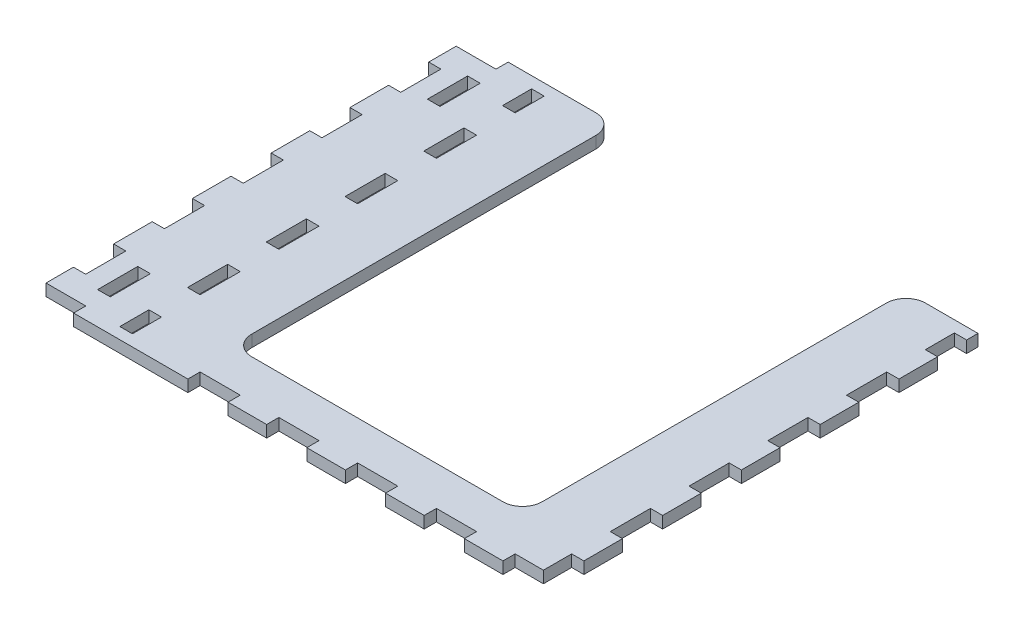
SolidWorks part; units mm, degrees
ref_plane "Front Plane" through (0, 0, 0) normal (0, 0, 1) x (1, 0, 0)
ref_plane "Top Plane" through (0, 0, 0) normal (0, 1, 0) x (1, 0, 0)
ref_plane "Right Plane" through (0, 0, 0) normal (1, 0, 0) x (0, 0, -1)
sketch "Sketch1" plane through (0, 0, 0) normal (0, 1, 0) x (1, 0, 0)
  line L0 (0, 0) -> (0, 21) construction
  line L1 (-114.8722, 48.0292) -> (-111.8722, 48.0292) construction
  line L2 (-66.1222, -11.6708) -> (-66.4222, -11.6708) construction
  line L3 (-66.4222, 40.2014) -> (-66.4222, -63.543) construction
  line L4 (-70.9222, -63.543) -> (-70.9222, 40.2014) construction
  line L5 (21.0585, -66.843) -> (-21.0585, -66.843) construction
  line L6 (-55.1722, 43.5014) -> (55.1722, 43.5014) construction
  line L7 (-55.1722, 43.5014) -> (-55.1722, -66.843) construction
  line L8 (-55.1722, -66.843) -> (55.1722, -66.843) construction
  line L9 (-66.4222, 43.5014) -> (-66.4222, -66.843) construction
  line L10 (-70.9222, -66.843) -> (-70.9222, 43.5014) construction
  line L11 (-70.9222, -11.6708) -> (-71.2222, -11.6708) construction
  line L12 (-55.1722, -63.843) -> (-74.2222, -63.843) construction
  line L13 (55.1722, 43.5014) -> (55.1722, -66.843)
  line L14 (-114.8722, -7.143) -> (-4.5278, -7.143) construction
  line L15 (36.8722, 43.5014) -> (36.8722, -66.843)
  line L16 (-36.8722, -66.843) -> (-36.8722, 43.5014)
  line L17 (36.8722, 99.9014) -> (36.8722, -3.843) construction
  line L18 (-55.1722, 43.5014) -> (-74.2222, 43.5014) construction
  line L19 (-74.2222, 43.5014) -> (-74.2222, -66.843)
  line L20 (-74.2222, -66.843) -> (-55.1722, -66.843) construction
  line L21 (-67.1722, 43.5014) -> (-67.1722, -66.843) construction
  line L22 (-70.1722, -66.843) -> (-70.1722, 43.5014) construction
  line L23 (-70.1722, -11.6708) -> (-67.1722, -11.6708) construction
  line L24 (-74.2222, -66.843) -> (-36.8722, -66.843)
  line L25 (-36.8722, -66.843) -> (-36.7807, -66.8623)
  line L26 (36.8722, -66.843) -> (55.1722, -66.843)
  line L27 (55.1722, 43.5014) -> (36.8722, 43.5014)
  line L28 (-71.2222, -66.843) -> (-71.2222, 43.5014) construction
  line L29 (-66.1222, -66.843) -> (-66.1222, 43.5014) construction
  line L30 (-74.2222, 40.5014) -> (-55.1722, 40.5014) construction
  line L31 (-63.1222, -66.843) -> (-63.1222, 43.5014) construction
  line L32 (-55.1722, -63.843) -> (55.1722, -63.843) construction
  line L33 (-36.8722, 43.5014) -> (-74.2222, 43.5014)
  line L34 (21.0585, -63.843) -> (-21.0585, -63.843) construction
  line L35 (0, -63.843) -> (0, -66.843) construction
  line L36 (-71.2222, -11.6708) -> (-74.2222, -11.6708) construction
  line L37 (-66.1222, -11.6708) -> (-63.1222, -11.6708) construction
  line L38 (-52.1722, -66.843) -> (-52.1722, 43.5014) construction
  line L39 (52.1722, -66.843) -> (52.1722, 43.5014) construction
  line L40 (52.1722, -11.6708) -> (55.1722, -11.6708) construction
  line L41 (-67.1722, -11.9708) -> (-55.1722, -11.9708) construction
  line L43 (-67.1722, -11.6708) -> (-55.1722, -11.6708) construction
  line L44 (-67.1722, -11.6708) -> (-66.8722, -11.6708) construction
  line L45 (-66.8722, -11.6708) -> (-66.8722, -11.9708) construction
  line L46 (0, -63.843) -> (0, -47.0292) construction
  line L47 (-35.0585, 12.9708) -> (-51.8722, 12.9708) construction
  line L48 (-35.0585, 12.9708) -> (-35.0585, 83.0877) construction
  line L49 (-35.0585, -47.0292) -> (35.0585, -47.0292) construction
  line L50 (-35.0585, -47.0292) -> (-35.0585, 23.0877) construction
  line L51 (-35.0585, 23.0877) -> (35.0585, 23.0877) construction
  line L52 (35.0585, -47.0292) -> (35.0585, 23.0877) construction
  line L53 (-36.8722, -48.843) -> (36.8722, -48.843) construction
  line L54 (35.0585, -47.0292) -> (35.0585, -48.843) construction
  line L55 (35.0585, -47.0292) -> (36.8722, -47.0292) construction
  circle A0 centre (0, 0) radius 21 construction
  circle A6 centre (0, 0) radius 21 construction
  dimension "D1" = 12
  dimension "D3" = 0.3
ref_plane "zplane" through (-67.1722, 0, 0) normal (1, 0, 0) x (0, 0, -1)
sketch "Sketch2" plane through (0, 0, 0) normal (0, 1, 0) x (1, 0, 0)
  line L0 (-74.2222, -66.843) -> (55.1722, -66.843)
  line L1 (-74.2222, -66.843) -> (-36.8722, -66.843) construction
  line L2 (-74.2222, -66.843) -> (-74.2222, 43.5014)
  line L3 (-74.2222, 43.5014) -> (-41.8722, 43.5014)
  line L4 (-36.8722, -66.843) -> (-36.8722, 43.5014) construction
  line L5 (41.8722, 43.5014) -> (55.1722, 43.5014)
  line L6 (36.8722, 43.5014) -> (36.8722, -66.843) construction
  line L7 (36.8722, -66.843) -> (55.1722, -66.843) construction
  line L8 (55.1722, 43.5014) -> (55.1722, -66.843)
  line L9 (-31.8722, -53.843) -> (31.8722, -53.843)
  line L10 (36.8722, -48.843) -> (36.8722, 38.5014)
  line L11 (-36.8722, -48.843) -> (-36.8722, 38.5014)
  line L12 (-36.8722, -48.843) -> (36.8722, -48.843) construction
  arc A0 (31.8722, -53.843) -> (36.8722, -48.843) centre (31.8722, -48.843) ccw
  arc A1 (-36.8722, -48.843) -> (-31.8722, -53.843) centre (-31.8722, -48.843) ccw
  arc A2 (41.8722, 43.5014) -> (36.8722, 38.5014) centre (41.8722, 38.5014) ccw
  arc A3 (-41.8722, 43.5014) -> (-36.8722, 38.5014) centre (-41.8722, 38.5014) cw
  point P16 (36.8722, -53.843)
  point P19 (-36.8722, -53.843)
  dimension "D1" = 5
  dimension "D3" = 5
  dimension "D2" = 13
extrude "Boss-Extrude1" add sketch "Sketch2" against normal up to vertex (3 mm away)
sketch "Sketch4" plane through (0, 0, 0) normal (0, 1, 0) x (1, 0, 0)
  line L0 (-74.2222, 43.5014) -> (-74.2222, -66.843) construction
  line L1 (-63.1222, -66.843) -> (-63.1222, 43.5014) construction
  line L2 (-71.2222, -66.843) -> (-71.2222, 43.5014) construction
  line L3 (-66.1222, -66.843) -> (-66.1222, 43.5014) construction
  line L4 (-74.2222, 43.5014) -> (-74.2222, -66.843) construction
  line L5 (-63.1222, -66.843) -> (-63.1222, 43.5014) construction
  line L6 (-71.2222, -66.843) -> (-71.2222, 43.5014) construction
  line L7 (-66.1222, -66.843) -> (-66.1222, 43.5014) construction
  line L8 (-74.2222, 40.5014) -> (-55.1722, 40.5014) construction
  line L9 (-36.8722, 43.5014) -> (-74.2222, 43.5014) construction
  line L10 (-74.2222, 40.5014) -> (-55.1722, 40.5014) construction
  line L11 (-36.8722, 43.5014) -> (-74.2222, 43.5014) construction
  line L12 (-74.2222, -66.843) -> (-36.8722, -66.843) construction
  line L13 (-55.1722, -63.843) -> (-74.2222, -63.843) construction
  line L14 (-74.2222, -66.843) -> (-36.8722, -66.843) construction
  line L15 (-55.1722, -63.843) -> (-74.2222, -63.843) construction
  line L16 (-55.1722, 33.3292) -> (-52.1722, 33.3292) construction
  line L17 (-55.1722, 23.3292) -> (-52.1722, 23.3292) construction
  line L18 (-55.1722, 13.3292) -> (-52.1722, 13.3292) construction
  line L19 (-55.1722, 3.3292) -> (-52.1722, 3.3292) construction
  line L20 (-55.1722, -6.6708) -> (-52.1722, -6.6708) construction
  line L21 (-55.1722, -16.6708) -> (-52.1722, -16.6708) construction
  line L22 (-55.1722, -56.6708) -> (-52.1722, -56.6708) construction
  line L23 (-55.1722, -46.6708) -> (-52.1722, -46.6708) construction
  line L24 (-55.1722, -36.6708) -> (-52.1722, -36.6708) construction
  line L25 (-55.1722, -26.6708) -> (-52.1722, -26.6708) construction
  line L26 (-74.2222, 33.3292) -> (-52.1722, 33.3292) construction
  line L27 (-74.2222, 23.3292) -> (-52.1722, 23.3292) construction
  line L28 (-74.2222, 13.3292) -> (-52.1722, 13.3292) construction
  line L29 (-74.2222, 3.3292) -> (-52.1722, 3.3292) construction
  line L30 (-74.2222, -6.6708) -> (-52.1722, -6.6708) construction
  line L31 (-74.2222, -16.6708) -> (-52.1722, -16.6708) construction
  line L32 (-74.2222, -56.6708) -> (-52.1722, -56.6708) construction
  line L33 (-74.2222, -46.6708) -> (-52.1722, -46.6708) construction
  line L34 (-74.2222, -36.6708) -> (-52.1722, -36.6708) construction
  line L35 (-74.2222, -26.6708) -> (-52.1722, -26.6708) construction
  line L36 (-66.1222, -48.543) -> (-63.1222, -48.543)
  line L37 (-66.1222, -58.543) -> (-63.1222, -58.543)
  line L38 (-64.6222, -48.543) -> (-64.6222, -58.543) construction
  line L39 (-52.1722, -46.6708) -> (-52.1722, -56.6708) construction
  line L40 (-66.1222, 25.2014) -> (-63.1222, 25.2014)
  line L41 (-66.1222, 35.2014) -> (-63.1222, 35.2014)
  line L42 (-64.6222, 35.2014) -> (-64.6222, 25.2014) construction
  line L43 (-52.1722, 43.5014) -> (-52.1722, -66.843) construction
  line L44 (-55.1722, 43.5014) -> (-55.1722, -66.843) construction
  line L45 (-55.1722, 43.5014) -> (-55.1722, -66.843) construction
  line L46 (-64.2222, -63.843) -> (-64.2222, -66.843)
  line L47 (-64.2222, 43.5014) -> (-64.2222, 40.5014)
  line L48 (-74.2222, 42.0014) -> (-64.2222, 42.0014) construction
sketch "Sketch3" plane through (0, 0, 0) normal (0, 1, 0) x (1, 0, 0)
  line L0 (52.1722, 40.5014) -> (-52.1722, 40.5014) construction
  line L1 (-74.3222, -66.943) -> (-74.3222, -63.743)
  line L2 (52.1722, 40.5014) -> (-52.1722, 40.5014) construction
  line L3 (52.0722, 40.4014) -> (52.0722, 40.5014) construction
  line L4 (-52.0722, 23.4292) -> (-55.2722, 23.4292)
  line L5 (-52.0722, 13.2292) -> (-52.0722, 23.4292)
  line L6 (-55.2722, 13.2292) -> (-52.0722, 13.2292)
  line L7 (-55.2722, 23.4292) -> (-55.2722, 13.2292)
  line L8 (-52.0722, 23.4292) -> (-55.2722, 23.4292)
  line L9 (-52.0722, 13.2292) -> (-52.0722, 23.4292)
  line L10 (-55.2722, 13.2292) -> (-52.0722, 13.2292)
  line L11 (-55.2722, 23.4292) -> (-55.2722, 13.2292)
  line L12 (-52.0722, 3.4292) -> (-55.2722, 3.4292)
  line L13 (-52.0722, -6.7708) -> (-52.0722, 3.4292)
  line L14 (-55.2722, -6.7708) -> (-52.0722, -6.7708)
  line L15 (-55.2722, 3.4292) -> (-55.2722, -6.7708)
  line L16 (-52.0722, 3.4292) -> (-55.2722, 3.4292)
  line L17 (-52.0722, -6.7708) -> (-52.0722, 3.4292)
  line L18 (-55.2722, -6.7708) -> (-52.0722, -6.7708)
  line L19 (-55.2722, 3.4292) -> (-55.2722, -6.7708)
  line L20 (-15.1, 43.6014) -> (-15.1, 40.4014)
  line L21 (-15.1, 40.4014) -> (-4.9, 40.4014)
  line L22 (-4.9, 40.4014) -> (-4.9, 43.6014)
  line L23 (-4.9, 43.6014) -> (-15.1, 43.6014)
  line L24 (-15.1, 43.6014) -> (-15.1, 40.4014) construction
  line L25 (-15.1, 40.4014) -> (-4.9, 40.4014) construction
  line L26 (-4.9, 40.4014) -> (-4.9, 43.6014) construction
  line L27 (-4.9, 43.6014) -> (-15.1, 43.6014) construction
  line L28 (-35.1, -63.743) -> (-35.1, -66.943)
  line L29 (-24.9, -63.743) -> (-35.1, -63.743)
  line L30 (-24.9, -66.943) -> (-24.9, -63.743)
  line L31 (-35.1, -66.943) -> (-24.9, -66.943)
  line L32 (-35.1, -63.743) -> (-35.1, -66.943)
  line L33 (-24.9, -63.743) -> (-35.1, -63.743)
  line L34 (-24.9, -66.943) -> (-24.9, -63.743)
  line L35 (-35.1, -66.943) -> (-24.9, -66.943)
  line L36 (-15.1, -63.743) -> (-15.1, -66.943)
  line L37 (-15.1, -66.943) -> (-4.9, -66.943)
  line L38 (-4.9, -66.943) -> (-4.9, -63.743)
  line L39 (-4.9, -63.743) -> (-15.1, -63.743)
  line L40 (-15.1, -63.743) -> (-15.1, -66.943)
  line L41 (-15.1, -66.943) -> (-4.9, -66.943)
  line L42 (-4.9, -66.943) -> (-4.9, -63.743)
  line L43 (-4.9, -63.743) -> (-15.1, -63.743)
  line L44 (-52.0722, 40.4014) -> (-24.9, 40.4014)
  line L45 (-52.0722, 40.4014) -> (-24.9, 40.4014) construction
  line L46 (-52.0722, 33.2292) -> (-52.0722, 40.4014)
  line L47 (-24.9, 40.4014) -> (-24.9, 43.6014)
  line L49 (-55.2722, 33.2292) -> (-52.0722, 33.2292)
  line L51 (-24.9, 40.4014) -> (-24.9, 43.6014) construction
  line L52 (35.1, -63.743) -> (24.9, -63.743)
  line L53 (24.9, -63.743) -> (24.9, -66.943)
  line L54 (-52.0722, 40.4014) -> (-24.9, 40.4014)
  line L55 (-52.0722, 40.4014) -> (-24.9, 40.4014) construction
  line L56 (-24.9, 40.4014) -> (-24.9, 43.6014)
  line L57 (-55.2722, 43.6014) -> (-55.2722, 33.2292)
  line L58 (-55.2722, 33.2292) -> (-52.0722, 33.2292)
  line L59 (-52.0722, 33.2292) -> (-52.0722, 40.4014)
  line L60 (-24.9, 40.4014) -> (-24.9, 43.6014) construction
  line L61 (-24.9, 43.6014) -> (-55.2722, 43.6014)
  line L62 (-24.9, 43.6014) -> (-55.2722, 43.6014) construction
  line L63 (-55.2722, 43.6014) -> (-55.2722, 33.2292) construction
  line L64 (-55.2722, 33.2292) -> (-52.0722, 33.2292)
  line L65 (-52.0722, 33.2292) -> (-52.0722, 40.4014) construction
  line L66 (24.9, -66.943) -> (35.1, -66.943)
  line L67 (35.1, -66.943) -> (35.1, -63.743)
  line L68 (35.1, -63.743) -> (24.9, -63.743)
  line L69 (24.9, -63.743) -> (24.9, -66.943)
  line L70 (24.9, -66.943) -> (35.1, -66.943)
  line L71 (35.1, -66.943) -> (35.1, -63.743)
  line L72 (-55.2722, -46.7708) -> (-52.0722, -46.7708)
  line L73 (-52.0722, -46.7708) -> (-52.0722, -36.5708)
  line L74 (-52.0722, -36.5708) -> (-55.2722, -36.5708)
  line L75 (-55.2722, -36.5708) -> (-55.2722, -46.7708)
  line L76 (-55.2722, -46.7708) -> (-52.0722, -46.7708)
  line L77 (-52.0722, -46.7708) -> (-52.0722, -36.5708)
  line L78 (-52.0722, -36.5708) -> (-55.2722, -36.5708)
  line L79 (-55.2722, -36.5708) -> (-55.2722, -46.7708)
  line L80 (-55.2722, -26.7708) -> (-52.0722, -26.7708)
  line L81 (-52.0722, -26.7708) -> (-52.0722, -16.5708)
  line L82 (-52.0722, -16.5708) -> (-55.2722, -16.5708)
  line L83 (-55.2722, -16.5708) -> (-55.2722, -26.7708)
  line L84 (-55.2722, -26.7708) -> (-52.0722, -26.7708)
  line L85 (-52.0722, -26.7708) -> (-52.0722, -16.5708)
  line L86 (-52.0722, -16.5708) -> (-55.2722, -16.5708)
  line L87 (-55.2722, -16.5708) -> (-55.2722, -26.7708)
  line L88 (52.0722, -16.5708) -> (52.0722, -26.7708)
  line L89 (55.2722, -16.5708) -> (52.0722, -16.5708)
  line L90 (-55.2722, -56.5708) -> (-52.0722, -56.5708)
  line L91 (-55.2722, -63.943) -> (-55.2722, -56.5708)
  line L92 (-52.0722, -63.943) -> (-55.2722, -63.943)
  line L93 (-52.0722, -56.5708) -> (-52.0722, -63.943)
  line L102 (52.0722, -56.5708) -> (52.0722, -63.743)
  line L103 (52.0722, -63.743) -> (44.9, -63.743)
  line L104 (44.9, -63.743) -> (44.9, -66.943)
  line L105 (44.9, -66.943) -> (55.2722, -66.943)
  line L106 (55.2722, -66.943) -> (55.2722, -56.5708)
  line L107 (55.2722, -56.5708) -> (52.0722, -56.5708)
  line L108 (52.0722, -56.5708) -> (52.0722, -63.743)
  line L109 (52.0722, -63.743) -> (44.9, -63.743)
  line L110 (44.9, -63.743) -> (44.9, -66.943)
  line L111 (44.9, -66.943) -> (55.2722, -66.943)
  line L112 (55.2722, -66.943) -> (55.2722, -56.5708)
  line L113 (55.2722, -56.5708) -> (52.0722, -56.5708)
  line L114 (55.2722, -26.7708) -> (55.2722, -16.5708)
  line L115 (52.0722, -26.7708) -> (55.2722, -26.7708)
  line L116 (52.0722, -16.5708) -> (52.0722, -26.7708)
  line L117 (55.2722, -16.5708) -> (52.0722, -16.5708)
  line L118 (55.2722, -26.7708) -> (55.2722, -16.5708)
  line L119 (52.0722, -26.7708) -> (55.2722, -26.7708)
  line L120 (52.0722, -36.5708) -> (52.0722, -46.7708)
  line L121 (55.2722, -36.5708) -> (52.0722, -36.5708)
  line L122 (55.2722, -46.7708) -> (55.2722, -36.5708)
  line L123 (52.0722, -46.7708) -> (55.2722, -46.7708)
  line L124 (52.0722, -36.5708) -> (52.0722, -46.7708)
  line L125 (55.2722, -36.5708) -> (52.0722, -36.5708)
  line L126 (55.2722, -46.7708) -> (55.2722, -36.5708)
  line L127 (52.0722, -46.7708) -> (55.2722, -46.7708)
  line L128 (4.9, -66.943) -> (15.1, -66.943)
  line L129 (4.9, -63.743) -> (4.9, -66.943)
  line L130 (15.1, -63.743) -> (4.9, -63.743)
  line L131 (15.1, -66.943) -> (15.1, -63.743)
  line L132 (4.9, -66.943) -> (15.1, -66.943)
  line L133 (4.9, -63.743) -> (4.9, -66.943)
  line L134 (15.1, -63.743) -> (4.9, -63.743)
  line L135 (15.1, -66.943) -> (15.1, -63.743)
  line L136 (4.9, 40.4014) -> (15.1, 40.4014)
  line L137 (4.9, 43.6014) -> (4.9, 40.4014)
  line L138 (15.1, 43.6014) -> (4.9, 43.6014)
  line L139 (15.1, 40.4014) -> (15.1, 43.6014)
  line L140 (4.9, 40.4014) -> (15.1, 40.4014) construction
  line L141 (4.9, 43.6014) -> (4.9, 40.4014) construction
  line L142 (15.1, 43.6014) -> (4.9, 43.6014) construction
  line L143 (15.1, 40.4014) -> (15.1, 43.6014) construction
  line L144 (24.9, 40.4014) -> (52.0722, 40.4014)
  line L145 (24.9, 43.6014) -> (24.9, 40.4014)
  line L146 (24.9, 40.4014) -> (52.0722, 40.4014) construction
  line L147 (52.0722, 40.4014) -> (52.0722, 33.2292)
  line L149 (24.9, 43.6014) -> (24.9, 40.4014) construction
  line L150 (52.0722, 33.2292) -> (55.2722, 33.2292)
  line L152 (55.2722, 23.4292) -> (52.0722, 23.4292)
  line L153 (52.0722, 23.4292) -> (52.0722, 13.2292)
  line L154 (52.0722, 13.2292) -> (55.2722, 13.2292)
  line L155 (55.2722, 13.2292) -> (55.2722, 23.4292)
  line L156 (55.2722, 23.4292) -> (52.0722, 23.4292)
  line L157 (52.0722, 23.4292) -> (52.0722, 13.2292)
  line L158 (52.0722, 13.2292) -> (55.2722, 13.2292)
  line L159 (55.2722, 13.2292) -> (55.2722, 23.4292)
  line L160 (55.2722, 3.4292) -> (52.0722, 3.4292)
  line L161 (55.2722, -6.7708) -> (55.2722, 3.4292)
  line L162 (52.0722, -6.7708) -> (55.2722, -6.7708)
  line L163 (52.0722, 3.4292) -> (52.0722, -6.7708)
  line L164 (55.2722, 3.4292) -> (52.0722, 3.4292)
  line L165 (55.2722, -6.7708) -> (55.2722, 3.4292)
  line L166 (52.0722, -6.7708) -> (55.2722, -6.7708)
  line L167 (52.0722, 3.4292) -> (52.0722, -6.7708)
  line L168 (52.0722, 40.5014) -> (52.0722, 40.6014) construction
  line L169 (52.0722, 33.2292) -> (52.0722, 40.6014)
  line L170 (24.9, 40.4014) -> (52.0722, 40.4014)
  line L171 (24.9, 40.4014) -> (52.0722, 40.4014) construction
  line L172 (52.0722, 40.4014) -> (52.0722, 33.2292)
  line L173 (52.0722, 33.2292) -> (55.2722, 33.2292)
  line L174 (55.2722, 33.2292) -> (55.2722, 43.6014)
  line L175 (24.9, 43.6014) -> (24.9, 40.4014)
  line L176 (24.9, 43.6014) -> (24.9, 40.4014) construction
  line L177 (55.2722, 43.6014) -> (24.9, 43.6014)
  line L178 (52.0722, 40.4014) -> (52.0722, 33.2292) construction
  line L179 (52.0722, 33.2292) -> (55.2722, 33.2292)
  line L180 (55.2722, 33.2292) -> (55.2722, 43.6014) construction
  line L181 (55.2722, 43.6014) -> (24.9, 43.6014) construction
  line L182 (52.0722, 40.6014) -> (55.2722, 40.6014)
  line L183 (55.2722, 40.6014) -> (55.2722, 33.2292)
  line L184 (0, -11.6708) -> (0, 43.5014) construction
  line L185 (0, -11.6708) -> (0, 43.5014) construction
  line L186 (-55.1722, -11.6708) -> (0, -11.6708) construction
  line L187 (-55.1722, -11.6708) -> (0, -11.6708) construction
  line L188 (-52.0722, 33.2292) -> (-52.0722, 40.6014)
  line L189 (-52.0722, 40.6014) -> (-55.2722, 40.6014)
  line L190 (-55.2722, 40.6014) -> (-55.2722, 33.2292)
  line L191 (-52.1722, 33.3292) -> (-52.1722, 33.2292) construction
  line L192 (-74.3222, 33.4292) -> (-71.1222, 33.4292)
  line L193 (-74.3222, 33.4292) -> (-74.3222, 23.2292)
  line L194 (-74.3222, 23.2292) -> (-71.1222, 23.2292)
  line L195 (-71.1222, 33.4292) -> (-71.1222, 23.2292)
  line L196 (-74.3222, 13.4292) -> (-71.1222, 13.4292)
  line L197 (-74.3222, 13.4292) -> (-74.3222, 3.2292)
  line L198 (-74.3222, 3.2292) -> (-71.1222, 3.2292)
  line L199 (-71.1222, 13.4292) -> (-71.1222, 3.2292)
  line L200 (-74.3222, -6.5708) -> (-71.1222, -6.5708)
  line L201 (-74.3222, -6.5708) -> (-74.3222, -16.7708)
  line L202 (-74.3222, -16.7708) -> (-71.1222, -16.7708)
  line L203 (-71.1222, -6.5708) -> (-71.1222, -16.7708)
  line L204 (-64.2222, 40.5014) -> (-64.1222, 40.5014) construction
  line L205 (-74.3222, 43.6014) -> (-64.1222, 43.6014)
  line L206 (-74.3222, 43.6014) -> (-74.3222, 40.4014)
  line L207 (-74.3222, 40.4014) -> (-64.1222, 40.4014)
  line L208 (-64.1222, 43.6014) -> (-64.1222, 40.4014)
  line L209 (-64.2222, 40.5014) -> (-64.2222, 40.4014) construction
  line L210 (-74.2222, 43.5014) -> (-74.3222, 43.5014) construction
  line L211 (-74.2222, 43.5014) -> (-74.2222, 43.6014) construction
  line L212 (-74.3222, -66.943) -> (-64.1222, -66.943)
  line L213 (-74.2222, 33.3292) -> (-74.2222, 33.4292) construction
  line L214 (-74.2222, 23.3292) -> (-74.2222, 23.2292) construction
  line L215 (-74.2222, 13.3292) -> (-74.2222, 13.4292) construction
  line L216 (-74.2222, 3.3292) -> (-74.2222, 3.2292) construction
  line L217 (-74.2222, -6.6708) -> (-74.2222, -6.5708) construction
  line L218 (-74.2222, -16.6708) -> (-74.2222, -16.7708) construction
  line L219 (-71.2222, 33.3292) -> (-71.1222, 33.3292) construction
  line L220 (-71.2222, -66.843) -> (-71.2222, 43.5014) construction
  line L221 (-64.1222, -66.943) -> (-64.1222, -63.743)
  line L222 (-74.3222, -63.743) -> (-64.1222, -63.743)
  line L223 (-66.2222, -58.643) -> (-63.0222, -58.643)
  line L224 (-63.0222, -58.643) -> (-63.0222, -48.443)
  line L225 (-66.2222, -48.443) -> (-63.0222, -48.443)
  line L226 (-66.1222, 35.2014) -> (-66.1222, 35.3014) construction
  line L227 (-66.2222, 35.3014) -> (-63.0222, 35.3014)
  line L228 (-66.2222, 35.3014) -> (-66.2222, 25.1014)
  line L229 (-66.2222, 25.1014) -> (-63.0222, 25.1014)
  line L230 (-63.0222, 35.3014) -> (-63.0222, 25.1014)
  line L231 (-66.1222, 35.2014) -> (-66.2222, 35.2014) construction
  line L232 (-63.1222, 25.2014) -> (-63.0222, 25.2014) construction
  line L233 (-63.1222, 25.2014) -> (-63.1222, 25.1014) construction
  line L234 (-66.2222, -58.643) -> (-66.2222, -48.443)
  line L235 (-74.3222, -56.7708) -> (-71.1222, -56.7708)
  line L236 (-74.3222, -56.7708) -> (-74.3222, -46.5708)
  line L237 (-74.3222, -46.5708) -> (-71.1222, -46.5708)
  line L238 (-71.1222, -56.7708) -> (-71.1222, -46.5708)
  line L239 (-74.3222, -36.7708) -> (-71.1222, -36.7708)
  line L240 (-74.3222, -36.7708) -> (-74.3222, -26.5708)
  line L241 (-74.3222, -26.5708) -> (-71.1222, -26.5708)
  line L242 (-71.1222, -36.7708) -> (-71.1222, -26.5708)
  line L595 (-55.2722, 43.6014) -> (-55.2722, 33.2292)
  line L597 (-24.9, 43.6014) -> (-55.2722, 43.6014)
  line L598 (-24.9, 43.6014) -> (-55.2722, 43.6014) construction
  line L755 (55.2722, 33.2292) -> (55.2722, 43.6014)
  line L757 (55.2722, 43.6014) -> (24.9, 43.6014)
  line L758 (55.2722, 43.6014) -> (24.9, 43.6014) construction
  dimension "D1" = 0
  dimension "D2" = 0
  dimension "D3" = 0
  dimension "D4" = 0
  dimension "D5" = 0
  dimension "D6" = 0
  dimension "D7" = 0
  dimension "D8" = 0
  dimension "D9" = 0
  dimension "D10" = 0
  dimension "D12" = 0
  dimension "D13" = 0
  dimension "D14" = 0
  dimension "D15" = 0
  dimension "D16" = 0
  dimension "D17" = 0
  dimension "D18" = 0
  dimension "D19" = 0
  dimension "D20" = 0
extrude "Cut-Extrude1" cut sketch "Sketch3" against normal through all
